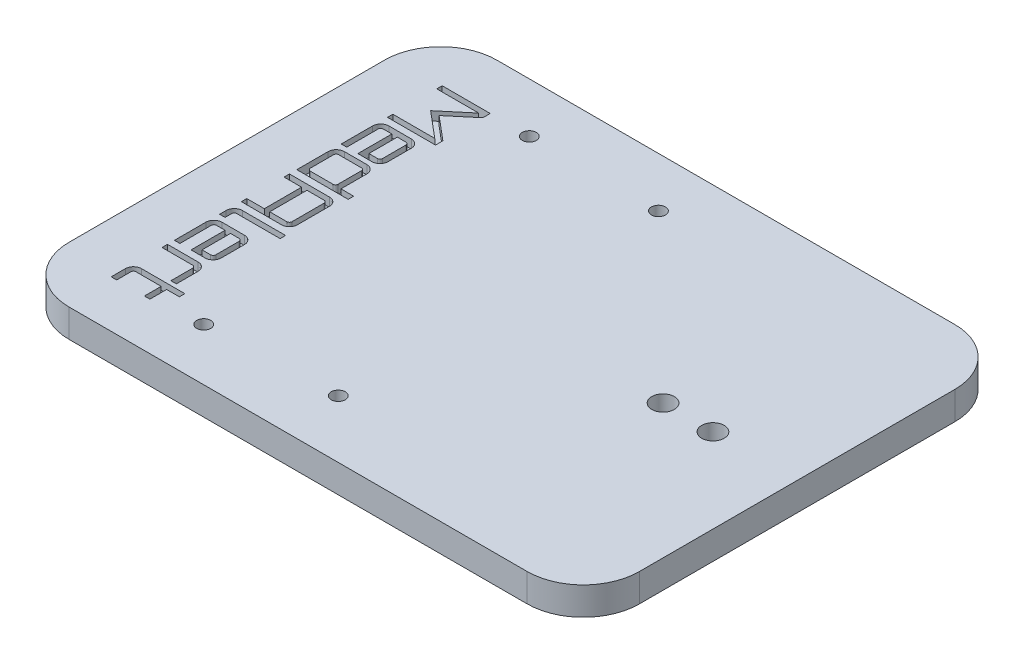
SolidWorks part; units mm, degrees
ref_plane "Front Plane" through (0, 0, 0) normal (0, 0, 1) x (1, 0, 0)
ref_plane "Top Plane" through (0, 0, 0) normal (0, 1, 0) x (1, 0, 0)
ref_plane "Right Plane" through (0, 0, 0) normal (1, 0, 0) x (0, 0, -1)
sketch "Sketch1" plane through (0, 0, 0) normal (0, 1, 0) x (1, 0, 0)
  line L1 (50.8, -38.1) -> (-50.8, -38.1)
  line L2 (50.8, -38.1) -> (50.8, 38.1)
  line L3 (50.8, 38.1) -> (-50.8, 38.1)
  line L4 (-50.8, -38.1) -> (-50.8, 38.1)
  line L5 (50.8, -38.1) -> (-50.8, 38.1) construction
  line L6 (50.8, 38.1) -> (-50.8, -38.1) construction
  point P0 (0, 0)
  dimension "D1" = 101.6
  dimension "D2" = 76.2
extrude "Boss-Extrude1" add sketch "Sketch1" along normal blind 5
sketch "Sketch2" plane through (0, 5, 0) normal (0, 1, 0) x (1, 0, 0)
  line L0 (-2.2581, 0) -> (2.2581, 0) construction
  line L1 (50.8, -38.1) -> (50.8, 38.1) construction
  circle A0 centre (35.8, 0) radius 2
  circle A1 centre (26.91, 0) radius 2
  dimension "D1" = 4
  dimension "D2" = 4
  dimension "D3" = 8.89
  dimension "D4" = 15
extrude "Cut-Extrude1" cut sketch "Sketch2" against normal through all
fillet "Fillet1" radius 10 4 edges at (-50.8, 2.5, -38.1) (-50.8, 2.5, 38.1) (50.8, 2.5, 38.1) (50.8, 2.5, -38.1)
sketch "Sketch4" plane through (0, 5, 0) normal (0, 1, 0) x (1, 0, 0)
  circle A0 centre (-3.1344, 29.2185) radius 1.25
  circle A1 centre (-3.1344, -27.8181) radius 1.25
  circle A2 centre (-26.1344, 29.2185) radius 1.25
  circle A3 centre (-26.1344, -28.7815) radius 1.25
  dimension "D1" = 2.5
  dimension "D2" = 2.5
  dimension "D3" = 2.5
  dimension "D4" = 2.5
  dimension "D5" = 23
  dimension "D6" = 23
  dimension "D7" = 58
extrude "Cut-Extrude2" cut sketch "Sketch4" against normal through all
sketch "Sketch5" plane through (0, 5, 0) normal (0, 1, 0) x (1, 0, 0)
  line L1 (-41.7142, 38.1) -> (-41.7142, -38.1) construction
  line L2 (40.8, 38.1) -> (-40.8, 38.1) construction
  line L3 (-40.8, -38.1) -> (40.8, -38.1) construction
  text T0 "MedAlert" font "Orbitron" height in points 24
extrude "Cut-Extrude3" cut sketch "Sketch5" against normal blind 1.5875
